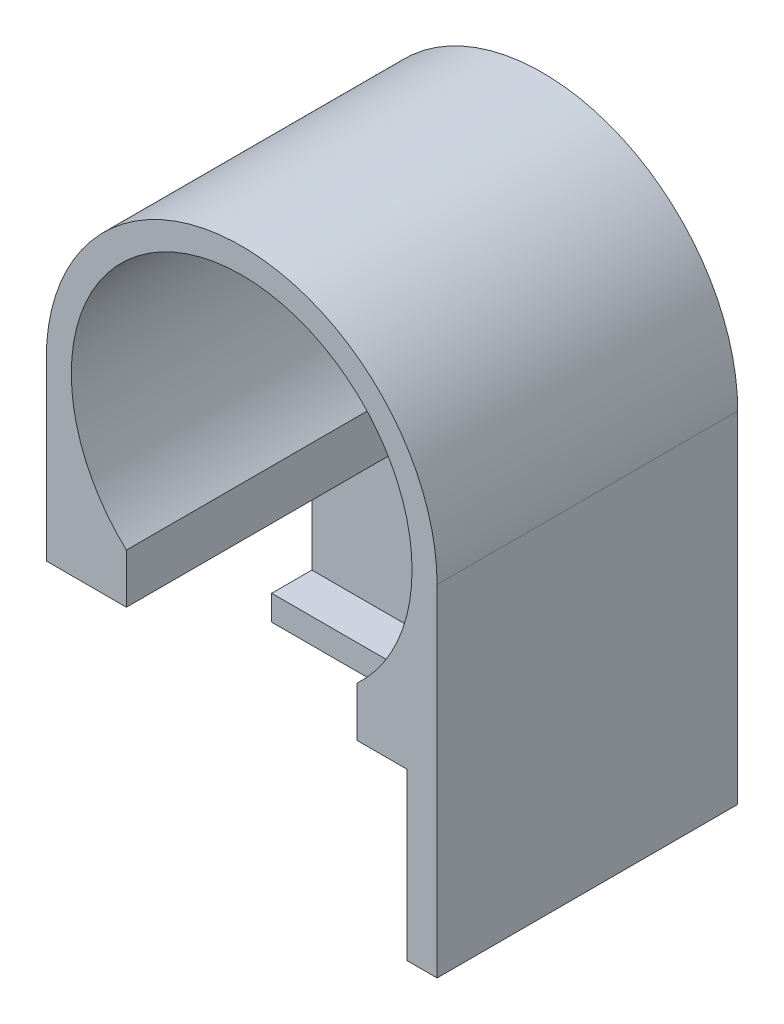
SolidWorks part; units mm, degrees
ref_plane "Front Plane" through (0, 0, 0) normal (0, 0, 1) x (1, 0, 0)
ref_plane "Top Plane" through (0, 0, 0) normal (0, 1, 0) x (1, 0, 0)
ref_plane "Right Plane" through (0, 0, 0) normal (1, 0, 0) x (0, 0, -1)
sketch "Sketch1" plane through (0, 0, 0) normal (0, 0, 1) x (1, 0, 0)
  circle A1 centre (0, 0) radius 43.18
  circle A2 centre (0, 0) radius 49.53
extrude "Boss-Extrude1" add sketch "Sketch1" along normal blind 76.2
sketch "Sketch2" plane through (0, 0, 0) normal (0, 0, 1) x (1, 0, 0)
  line L2 (-49.53, 0) -> (-49.53, -49.53)
  line L7 (0, -86.36) -> (-49.53, -86.36)
  line L8 (-49.53, -86.36) -> (-49.53, -49.53)
  line L10 (49.53, 0) -> (49.53, -86.36)
  line L11 (49.53, -86.36) -> (0, -86.36)
  circle A2 centre (0, 0) radius 49.53
extrude "Boss-Extrude2" add sketch "Sketch2" along normal blind 76.2 contours A2 L2 L8 L7 L11 L10
sketch "Sketch3" plane through (-49.53, 0, 0) normal (-1, 0, 0) x (0, 0, 1)
  line L0 (0, -86.36) -> (76.2, -86.36)
  line L1 (76.2, -86.36) -> (76.2, 0)
  line L2 (76.2, 0) -> (0, 0)
  line L3 (0, 0) -> (0, -86.36)
  line L4 (0, -86.36) -> (31.7689, -86.36)
  line L7 (0, -86.36) -> (6.4099, -86.36)
  line L8 (0, -86.36) -> (0, -43.18)
  line L9 (0, -86.36) -> (0, -80.01)
  line L10 (8.8798, -80.01) -> (19.0651, -80.01)
  line L11 (0, -86.36) -> (19.0651, -86.36)
  line L12 (19.0651, -86.36) -> (19.0651, -80.01)
  line L13 (8.8798, -80.01) -> (8.8798, -44.3564)
  line L14 (0, -86.36) -> (19.0651, -86.36)
  line L16 (76.2, -86.36) -> (19.0651, -86.36)
  line L17 (0, -43.18) -> (0, -44.3564)
  line L18 (0, -44.3564) -> (76.2, -44.3564)
  line M8 (0, -86.36) -> (76.2, -86.36)
  line M9 (76.2, -86.36) -> (76.2, 0)
extrude "Cut-Extrude4" cut sketch "Sketch3" against normal blind 91.44 contours L18 L13 L10 L12 L0 M8 M9
sketch "Sketch6" plane through (0, -44.3564, 0) normal (0, -1, 0) x (1, 0, 0)
  line L1 (-29.21, 76.2) -> (29.21, 76.2)
  line L7 (0, 76.2) -> (29.21, 76.2)
  line L12 (-29.21, 6.3202) -> (29.21, 6.3202)
  line L13 (-29.21, 76.2) -> (29.21, 76.2)
  line L14 (29.21, 76.2) -> (29.21, 6.3202)
  line L15 (-29.21, 76.2) -> (29.21, 76.2)
  line L16 (0, 76.2) -> (-29.21, 76.2)
  line L18 (-29.21, 76.2) -> (-29.21, 6.3202)
  line M10 (-49.53, 8.8798) -> (41.91, 8.8798)
  line M12 (41.91, 76.2) -> (-49.53, 76.2)
extrude "Cut-Extrude5" cut sketch "Sketch6" against normal blind 23.622 and the other way blind 20.066 from offset 0 contours L1 L18 L14 M10 M12
